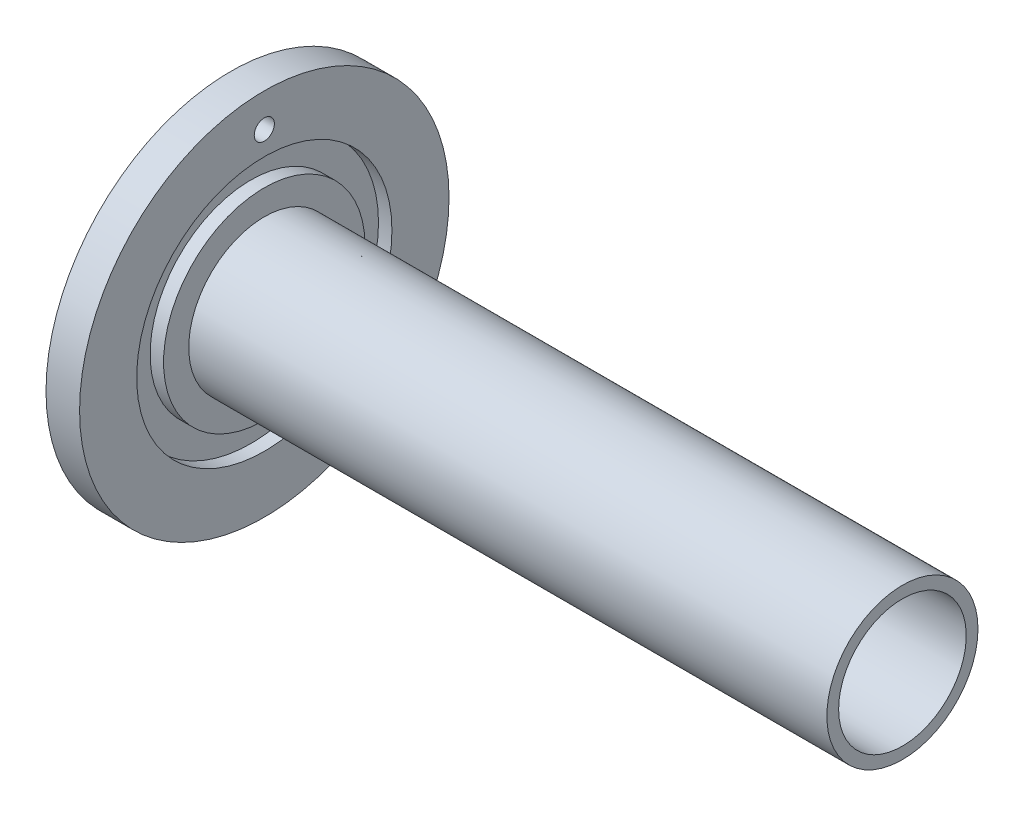
SolidWorks part; units mm, degrees
ref_plane "Front Plane" through (0, 0, 0) normal (0, 0, 1) x (1, 0, 0)
ref_plane "Top Plane" through (0, 0, 0) normal (0, 1, 0) x (1, 0, 0)
ref_plane "Right Plane" through (0, 0, 0) normal (1, 0, 0) x (0, 0, -1)
sketch "Sketch2" plane through (0, 0, 0) normal (1, 0, 0) x (0, 0, -1)
  circle A0 centre (0, 0) radius 55
extrude "Boss-Extrude1" add sketch "Sketch2" along normal blind 10
sketch "Sketch3" plane through (10, 0, 0) normal (1, 0, 0) x (0, 0, -1)
  circle A0 centre (0, 0) radius 22.5
extrude "Boss-Extrude2" add sketch "Sketch3" along normal blind 190
sketch "Sketch4" plane through (0, 0, 0) normal (-1, 0, 0) x (0, 0, 1)
  circle A0 centre (0, 0) radius 19
extrude "Cut-Extrude1" cut sketch "Sketch4" against normal through all both and the other way through all
sketch "Sketch14" plane through (0, 0, 0) normal (-1, 0, 0) x (0, 0, 1)
  circle A0 centre (0, 0) radius 30.5
  circle A1 centre (0, 0) radius 37.5
sketch "Sketch15" plane through (10, 0, 0) normal (1, 0, 0) x (0, 0, -1)
  circle A0 centre (0, 0) radius 30
  circle A1 centre (0, 0) radius 38
extrude "Cut-Extrude5" cut sketch "Sketch14" against normal blind 1
extrude "Cut-Extrude6" cut sketch "Sketch15" against normal blind 4
sketch "Sketch16" plane through (0, 0, 0) normal (-1, 0, 0) x (0, 0, 1)
  circle A0 centre (0, 34) radius 2.5
  circle A1 centre (0, -34) radius 2.5
extrude "Cut-Extrude7" cut sketch "Sketch16" against normal blind 4
sketch "Sketch17" plane through (0, 0, 0) normal (-1, 0, 0) x (0, 0, 1)
  circle A0 centre (0, -34) radius 5
  circle A1 centre (0, 34) radius 5
extrude "Cut-Extrude8" cut sketch "Sketch17" against normal blind 2
sketch "Sketch20" plane through (0, 0, 0) normal (-1, 0, 0) x (0, 0, 1)
  circle A0 centre (-26, 0) radius 3
extrude "Cut-Extrude9" cut sketch "Sketch20" against normal blind 10
sketch "Sketch21" plane through (0, 0, 0) normal (-1, 0, 0) x (0, 0, 1)
  circle A0 centre (0, 45) radius 3
  point P2 (0, 0)
extrude "Cut-Extrude10" cut sketch "Sketch21" against normal blind 10
